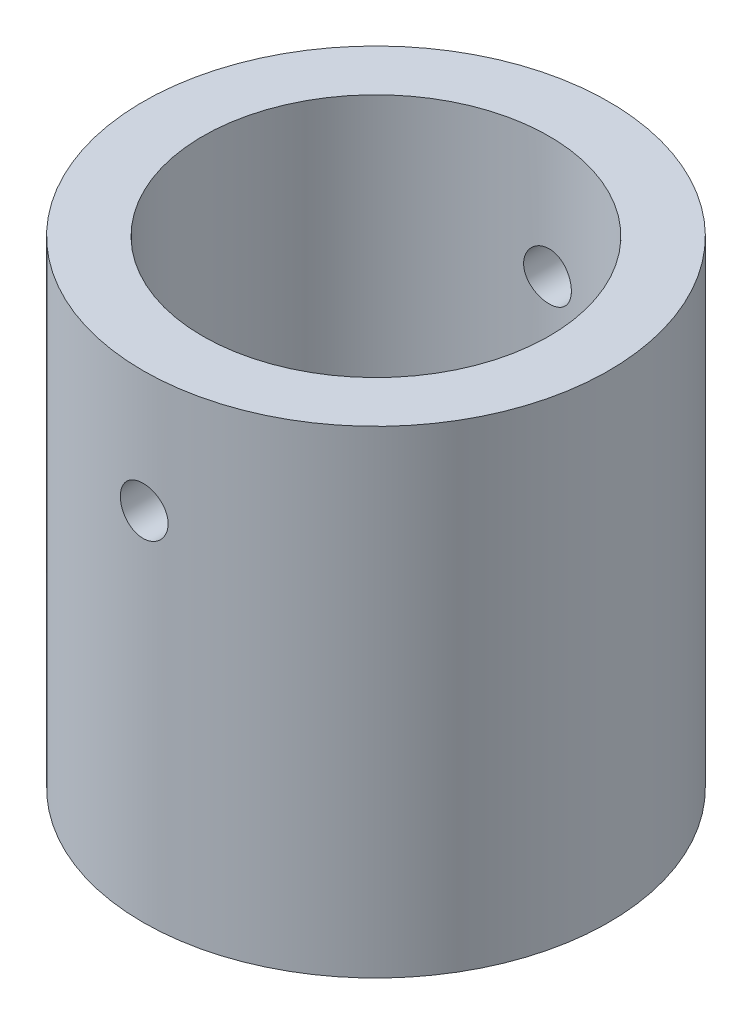
SolidWorks part; units mm, degrees
ref_plane "Front Plane" through (0, 0, 0) normal (0, 0, 1) x (1, 0, 0)
ref_plane "Top Plane" through (0, 0, 0) normal (0, 1, 0) x (1, 0, 0)
ref_plane "Right Plane" through (0, 0, 0) normal (1, 0, 0) x (0, 0, -1)
sketch "Sketch1" plane through (0, 0, 0) normal (0, 1, 0) x (1, 0, 0)
  circle A0 centre (0, 0) radius 14.5
  circle A1 centre (0, 0) radius 19.5
  dimension "D1" = 29
  dimension "D2" = 5
extrude "Boss-Extrude1" add sketch "Sketch1" along normal blind 40
ref_plane "Plane1" through (0, 0, 19.5) normal (0, 0, 1) x (1, 0, 0)
sketch "Sketch2" plane through (0, 0, 19.5) normal (0, 0, 1) x (1, 0, 0)
  line L0 (-19.5, 0) -> (19.5, 0) construction
  circle A0 centre (0, 29.84) radius 2
  point P0 (0, 29.84)
  dimension "D2" = 4
  dimension "D1" = 29.84
extrude "Cut-Extrude1" cut sketch "Sketch2" against normal blind 42
